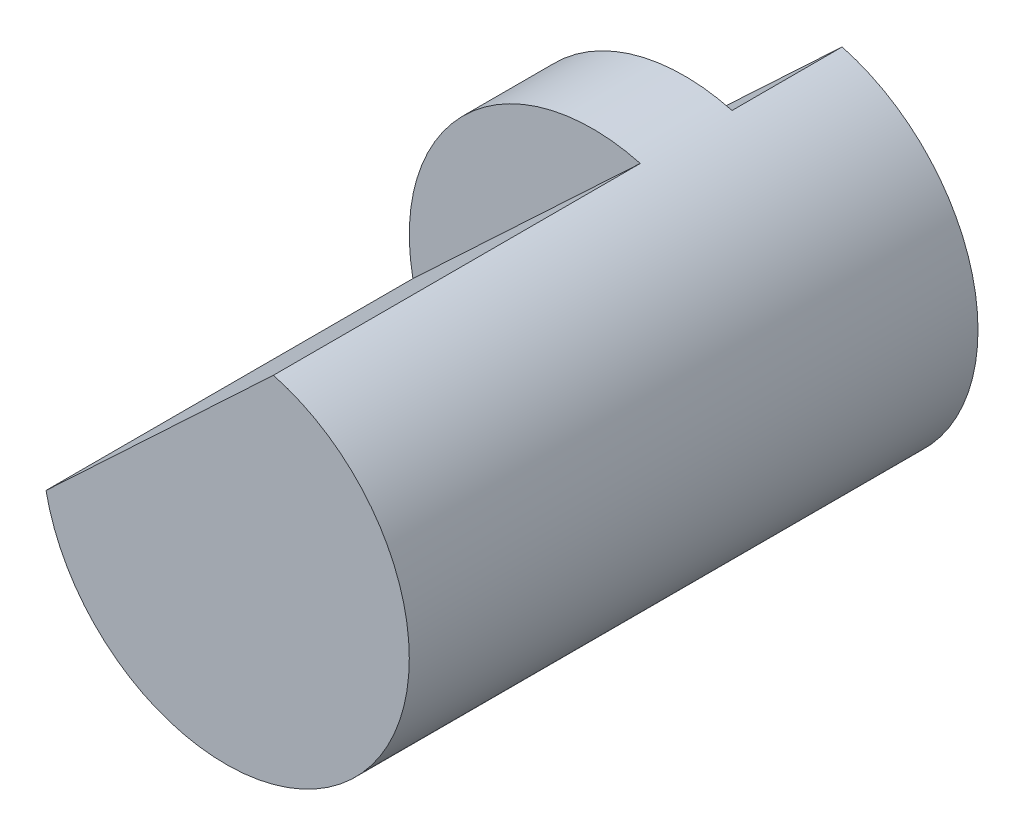
SolidWorks part; units mm, degrees
ref_plane "Front Plane" through (0, 0, 0) normal (0, 0, 1) x (1, 0, 0)
ref_plane "Top Plane" through (0, 0, 0) normal (0, 1, 0) x (1, 0, 0)
ref_plane "Right Plane" through (0, 0, 0) normal (1, 0, 0) x (0, 0, -1)
sketch "Sketch1" plane through (0, 0, 0) normal (0, 0, 1) x (1, 0, 0)
  line L0 (-9.8029, -1.9759) -> (2.5928, 9.658)
  arc A0 (-9.8029, -1.9759) -> (2.5928, 9.658) centre (0, 0) ccw
  dimension "D1" = 20
  dimension "D2" = 17
extrude "Boss-Extrude1" add sketch "Sketch1" along normal blind 19
ref_plane "Plane1" through (0, 0, 6) normal (0, 0, -1) x (-1, 0, 0)
sketch "Sketch2" plane through (0, 0, 6) normal (0, 0, -1) x (-1, 0, 0)
  line L0 (-2.5928, 9.658) -> (9.8029, -1.9759)
  line L1 (-2.5928, 9.658) -> (9.8029, -1.9759) construction
  arc A0 (9.8029, -1.9759) -> (-2.5928, 9.658) centre (0, 0) ccw
  arc A1 (-2.5928, 9.658) -> (9.8029, -1.9759) centre (0, 0) ccw construction
extrude "Boss-Extrude2" add sketch "Sketch2" against normal through all
sketch "Sketch4" plane through (0, 0, 19) normal (0, 0, 1) x (1, 0, 0)
  line L0 (2.5928, 9.658) -> (-9.8029, -1.9759)
  arc A0 (-9.8029, -1.9759) -> (2.5928, 9.658) centre (0, 0) ccw
extrude "Boss-Extrude4" add sketch "Sketch4" along normal blind 12
sketch "Sketch5" plane through (0, 0, 19) normal (0, 0, 1) x (1, 0, 0)
  line L0 (2.5928, 9.658) -> (-9.8029, -1.9759)
  arc A0 (2.5928, 9.658) -> (-9.8029, -1.9759) centre (0, 0) ccw
extrude "Cut-Extrude1" cut sketch "Sketch5" against normal blind 8
